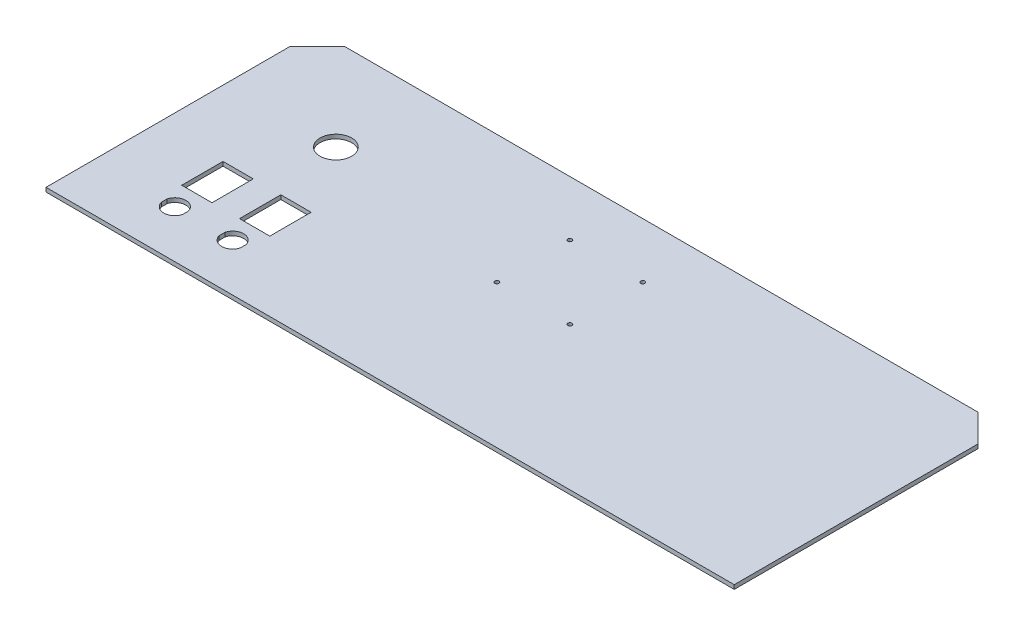
SolidWorks part; units mm, degrees
ref_plane "Front Plane" through (0, 0, 0) normal (0, 0, 1) x (1, 0, 0)
ref_plane "Top Plane" through (0, 0, 0) normal (0, 1, 0) x (1, 0, 0)
ref_plane "Right Plane" through (0, 0, 0) normal (1, 0, 0) x (0, 0, -1)
sketch "Sketch1" plane through (0, 0, 0) normal (0, 1, 0) x (1, 0, 0)
  line L0 (219.0695, 78.55) -> (219.0695, -98.55)
  line L1 (219.0695, -98.55) -> (-280.9305, -98.55)
  line L2 (-280.9305, -98.55) -> (-280.9305, 78.55)
  line L3 (-280.9305, 78.55) -> (-260.9305, 98.55)
  line L4 (-260.9305, 98.55) -> (199.0695, 98.55)
  line L5 (199.0695, 98.55) -> (219.0695, 78.55)
extrude "Boss-Extrude1" add sketch "Sketch1" along normal blind 3
sketch "Sketch2" plane through (0, 3, 0) normal (0, 1, 0) x (1, 0, 0)
  line L1 (199.0695, 98.55) -> (-260.9305, 98.55) construction
  line L3 (-4.4305, 58.55) -> (-57.4305, 58.55)
  line L4 (-57.4305, 58.55) -> (-57.4305, 5.55)
  line L5 (-57.4305, 5.55) -> (-4.4305, 5.55)
  line L6 (-4.4305, 5.55) -> (-4.4305, 58.55)
  line L8 (-30.9305, 98.55) -> (-30.9305, 58.55)
  circle A0 centre (-4.4305, 5.55) radius 1.5
  circle A1 centre (-57.4305, 5.55) radius 1.5
  circle A2 centre (-57.4305, 58.55) radius 1.5
  circle A3 centre (-4.4305, 58.55) radius 1.5
extrude "Cut-Extrude1" cut sketch "Sketch2" against normal up to surface (3 mm away) contours A0 | A3 | A2 | A1 up to face at (-30.9305, 0, -26.1833)
sketch "Sketch3" plane through (0, 3, 0) normal (0, 1, 0) x (1, 0, 0)
  line L0 (-210.9305, -47.95) -> (-232.9305, -47.95)
  line L1 (-232.9305, -47.95) -> (-232.9305, -17.95)
  line L2 (-280.9305, 78.55) -> (-280.9305, -98.55) construction
  line L3 (-280.9305, 32.05) -> (-200.9305, 32.05)
  line L4 (-232.9305, -17.95) -> (-210.9305, -17.95)
  line L5 (-210.9305, -17.95) -> (-210.9305, -47.95)
  line L6 (-200.9305, 32.05) -> (-200.9305, -17.95)
  line L7 (-190.9305, -17.95) -> (-210.9305, -17.95)
  line L8 (-168.9305, -47.95) -> (-190.9305, -47.95)
  line L9 (-190.9305, -47.95) -> (-190.9305, -17.95)
  line L10 (-190.9305, -17.95) -> (-168.9305, -17.95)
  line L11 (-168.9305, -17.95) -> (-168.9305, -47.95)
  circle A2 centre (-200.9305, 32.05) radius 11.5
extrude "Cut-Extrude2" cut sketch "Sketch3" against normal up to surface (3 mm away) contours L10 L11 L8 L9 | L5 L0 L1 L4 | A2 up to face at (-57.4305, 0, -4.05)
sketch "Sketch4" plane through (0, 3, 0) normal (0, 1, 0) x (1, 0, 0)
  line L0 (-179.9305, -47.95) -> (-179.9305, -55.95)
  line L1 (-168.9305, -47.95) -> (-190.9305, -47.95) construction
  line L2 (-221.9305, -47.95) -> (-221.9305, -55.95)
  line L3 (-210.9305, -47.95) -> (-232.9305, -47.95) construction
  line L4 (-187.6305, -63.95) -> (-187.9305, -63.95)
  line L5 (-187.6305, -63.95) -> (-187.6305, -66.1203)
  line L6 (-171.9305, -63.95) -> (-172.2305, -63.95)
  line L7 (-172.2305, -63.95) -> (-172.2305, -66.1203)
  line L8 (-172.2305, -63.95) -> (-172.2305, -61.7797)
  line L9 (-187.6305, -63.95) -> (-187.6305, -61.7797)
  line L10 (-229.6305, -63.95) -> (-229.9305, -63.95)
  line L11 (-213.9305, -63.95) -> (-214.2305, -63.95)
  line L12 (-229.6305, -63.95) -> (-229.6305, -66.1203)
  line L13 (-214.2305, -63.95) -> (-214.2305, -66.1203)
  line L14 (-229.6305, -63.95) -> (-229.6305, -61.7797)
  line L15 (-214.2305, -63.95) -> (-214.2305, -61.7797)
  circle A1 centre (-179.9305, -63.95) radius 8
  circle A2 centre (-221.9305, -63.95) radius 8
extrude "Cut-Extrude3" cut sketch "Sketch4" against normal up to surface (3 mm away) contours A1 | A2
